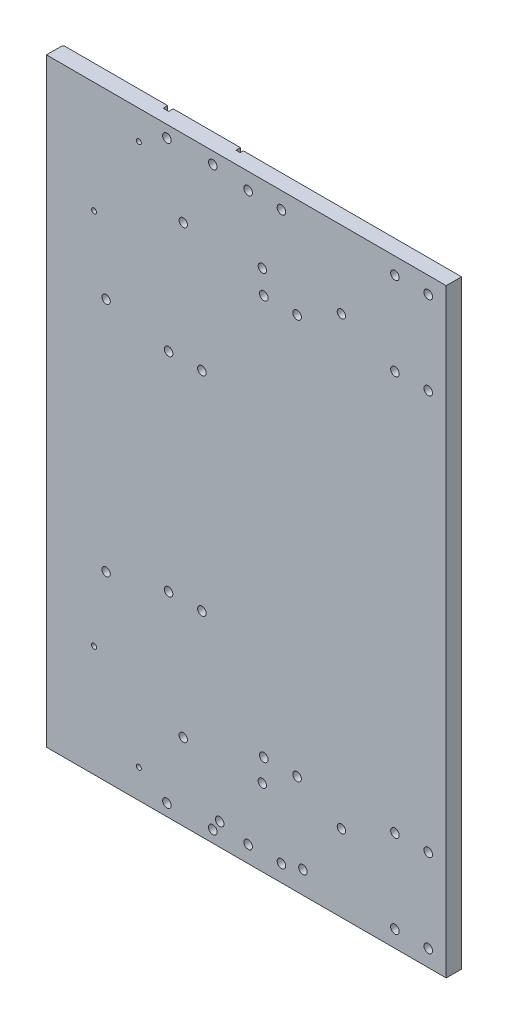
SolidWorks part; units mm, degrees
ref_plane "Front" through (0, 0, 0) normal (0, 0, 1) x (1, 0, 0)
ref_plane "Top" through (0, 0, 0) normal (0, 1, 0) x (1, 0, 0)
ref_plane "Right" through (0, 0, 0) normal (1, 0, 0) x (0, 0, -1)
sketch "Sketch1" plane through (0, 0, 0) normal (0, 0, 1) x (1, 0, 0)
  line L1 (-152.4, -228.6) -> (152.4, -228.6)
  line L2 (-152.4, -228.6) -> (-152.4, 228.6)
  line L3 (-152.4, 228.6) -> (152.4, 228.6)
  line L4 (152.4, -228.6) -> (152.4, 228.6)
  line L5 (-152.4, -228.6) -> (152.4, 228.6) construction
  line L6 (-152.4, 228.6) -> (152.4, -228.6) construction
  point P0 (0, 0)
  dimension "D1" = 304.8
  dimension "D2" = 457.2
extrude "Extrude1" add sketch "Sketch1" along normal blind 12.7
hole_wizard "5/16-18 Tapped Hole1" positions "3DSketch4" profile "Sketch7" tap size "5/16-18" standard "Ansi Inch" end condition up to next
sketch3d "3DSketch4"
  line L0 (1.364, 215.9, 0) -> (26.764, 215.9, 0) construction
  line L1 (14.064, 215.9, 0) -> (14.064, 92.8691, 0) construction
  line L3 (-152.4, 228.6, 0) -> (-152.4, -228.6, 0) construction
  point P0 (1.364, 215.9, 0)
  point P2 (26.764, 215.9, 0)
  dimension "D1" = 153.764
  dimension "D2" = 25.4
  dimension "D3" = 215.9
sketch "Sketch7" plane through (1.364, 215.9, 0) normal (1, 0, 0) x (0, 1, 0)
  line L0 (0, 0) -> (0, 12.701)
  line L1 (0, 12.701) -> (3.2639, 12.701)
  line L2 (3.2639, 12.701) -> (3.2639, 1.3398)
  line L3 (3.2639, 1.3398) -> (4.6037, 0)
  line L5 (4.6037, 0) -> (0, 0)
  line L6 (-3.2639, 1.3398) -> (-4.6037, 0) construction
  line L11 (0, -6.35) -> (0, 107.95) construction
  dimension "Thru Tap Drill Dia." = 6.5278
  dimension "Thru Tap Drill Depth" = 12.701
  dimension "Near C'Sink Dia." = 9.2075
  dimension "Near C'Sink Angle" = 90
cosmetic thread "Hole Thread9" parameters "D2"=7.9375
cosmetic thread "Hole Thread10" parameters "D2"=7.9375
hole_wizard "1/4 (0.25) Diameter Hole2" positions "3DSketch5" profile "Sketch9" hole size "1/4" standard "Ansi Inch"
sketch3d "3DSketch5"
  line L0 (-117.475, 198.2216, 0) -> (-136.525, 198.2216, 0) construction
  line L1 (-117.475, 198.2216, 0) -> (-117.475, 198.2216, 1.2573) construction
  line L2 (-136.525, 198.2216, 0) -> (-136.525, 198.2216, 1.2573) construction
  point P0 (-127, 198.2216, 0)
sketch "Sketch9" plane through (-127, 198.2216, 0) normal (1, 0, 0) x (0, 1, 0)
  line L0 (0, 0) -> (0, 12.701)
  line L1 (0, 12.701) -> (3.175, 12.701)
  line L2 (3.175, 12.701) -> (3.175, 0.381)
  line L3 (3.175, 0.381) -> (3.556, 0)
  line L5 (3.556, 0) -> (0, 0)
  line L6 (-3.175, 0.381) -> (-3.556, 0) construction
  line L11 (0, -6.35) -> (0, 107.95) construction
  dimension "Thru Hole Dia." = 6.35
  dimension "Thru Hole Depth" = 12.701
  dimension "Near C'Sink Dia." = 7.112
  dimension "Near C'Sink Angle" = 90
mirror "Mirror2" about plane through (0, 0, 0) normal (0, 1, 0) of "1/4 (0.25) Diameter Hole2", "5/16-18 Tapped Hole1"
sketch "Sketch10" plane through (0, 0, 0) normal (0, 0, -1) x (-1, 0, 0)
  line L0 (56.9694, -193.0028) -> (101.6133, -217.2425)
  line L2 (152.4, -188.6) -> (125.1873, -173.8247) construction
  line L4 (101.6133, -217.2425) -> (125.1873, -173.8247) construction
  line L5 (152.4, 228.6) -> (152.4, -228.6) construction
  line L6 (152.4, -228.6) -> (-152.4, -228.6) construction
  dimension "D1" = 61.5
  dimension "D2" = 40
  dimension "D3" = 50.8
  dimension "D4" = 30.9652
  dimension "D5" = 49.4048
extrude "Cut-Extrude-Thin1" cut sketch "Sketch10" against normal blind 6 thin thin type mid plane wall 10.16
sketch "Sketch11" plane through (0, 0, 0) normal (0, 0, -1) x (-1, 0, 0)
  line L0 (23.1752, -133.9492) -> (126.1356, -189.8522) construction
  line L1 (88.6834, -134.5929) -> (93.5313, -125.6642)
  line L2 (133.3273, -158.8326) -> (88.6834, -134.5929)
  line L3 (138.1752, -149.9038) -> (133.3273, -158.8326)
  line L4 (54.5454, -197.4672) -> (99.1894, -221.7069)
  line L5 (99.1894, -221.7069) -> (104.0373, -212.7781)
  line L6 (104.0373, -212.7781) -> (59.3934, -188.5384)
  line L7 (59.3934, -188.5384) -> (54.5454, -197.4672)
  line L8 (54.5454, -197.4672) -> (99.1894, -221.7069)
  line L9 (99.1894, -221.7069) -> (104.0373, -212.7781)
  line L10 (104.0373, -212.7781) -> (59.3934, -188.5384)
  line L11 (59.3934, -188.5384) -> (54.5454, -197.4672)
  line L12 (93.5313, -125.6642) -> (138.1752, -149.9038)
  dimension "D2" = 71.5442
  dimension "D1" = 0
extrude "Cut-Extrude1" cut sketch "Sketch11" against normal blind 6
hole_wizard "#10-24 Tapped Hole1" positions "Sketch13" profile "Sketch12" tap size "#10-24" standard "Ansi Inch" end condition through all
sketch "Sketch13" plane through (0, 0, 6) normal (0, 0, -1) x (-1, 0, 0)
  line L0 (101.6133, -217.2425) -> (81.97, -206.577)
  line L1 (104.0373, -212.7781) -> (99.1894, -221.7069) construction
  line L2 (81.97, -206.577) -> (116.1079, -143.7028) construction
  line L3 (135.7513, -154.3682) -> (116.1079, -143.7028) construction
  line L4 (133.3273, -158.8326) -> (138.1752, -149.9038) construction
  point P0 (81.97, -206.577)
  point P7 (116.1079, -143.7028)
  dimension "D1" = 22.352
sketch "Sketch12" plane through (-81.97, -206.577, 6) normal (1, 0, 0) x (0, 1, 0)
  line L0 (0, 0) -> (0, 6.7)
  line L1 (0, 6.7) -> (1.8986, 6.7)
  line L2 (1.8986, 6.7) -> (1.8986, 1.1494)
  line L3 (1.8986, 1.1494) -> (3.048, 0)
  line L5 (3.048, 0) -> (0, 0)
  line L6 (-1.8986, 1.1493) -> (-3.048, 0) construction
  line L11 (0, -6.35) -> (0, 107.95) construction
  dimension "Thru Tap Drill Dia." = 3.7973
  dimension "Thru Tap Drill Depth" = 6.7
  dimension "Near C'Sink Dia." = 6.096
  dimension "Near C'Sink Angle" = 90
cosmetic thread "Hole Thread11" parameters "D2"=4.826
cosmetic thread "Hole Thread12" parameters "D2"=4.826
fillet "Fillet1" radius 3.175 8 edges at (-133.3273, -158.8326, 3) (-138.1752, -149.9038, 3) (-104.0373, -212.7781, 3) (-99.1894, -221.7069, 3) (-88.6834, -134.5929, 3) (-93.5313, -125.6642, 3) (-59.3934, -188.5384, 3) (-54.5454, -197.4672, 3)
mirror "Mirror3" about plane through (0, 0, 0) normal (0, 1, 0) of "Cut-Extrude-Thin1", "Cut-Extrude1", "#10-24 Tapped Hole1", "Fillet1"
hole_wizard "5/16-18 Tapped Hole2" positions "Sketch15" profile "Sketch14" tap size "5/16-18" standard "Ansi Inch"
sketch "Sketch15" plane through (0, 0, 0) normal (0, 0, -1) x (-1, 0, 0)
  line L0 (-43.18, -211.6) -> (20.32, -211.6) construction
  line L1 (152.4, -228.6) -> (-152.4, -228.6) construction
  line L2 (152.4, 228.6) -> (152.4, -228.6) construction
  point P0 (-43.18, -211.6)
  point P1 (20.32, -211.6)
  dimension "D1" = 63.5
  dimension "D2" = 17
  dimension "D3" = 132.08
sketch "Sketch14" plane through (43.18, -211.6, 0) normal (1, 0, 0) x (0, 1, 0)
  line L0 (0, 0) -> (0, 34.4223)
  line L1 (0, 34.4223) -> (3.2639, 32.4612)
  line L2 (3.2639, 32.4612) -> (3.2639, 1.3399)
  line L3 (3.2639, 1.3399) -> (4.6037, 0)
  line L5 (4.6037, 0) -> (0, 0)
  line L6 (-3.2639, 1.3399) -> (-4.6037, 0) construction
  line L10 (0, 34.4223) -> (-3.2639, 32.4612) construction
  line L11 (0, -6.35) -> (0, 107.95) construction
  dimension "Tap Drill Dia." = 6.5278
  dimension "Tap Drill Depth" = 32.4612
  dimension "Near C'Sink Dia." = 9.2075
  dimension "Near C'Sink Angle" = 90
  dimension "Drill Angle" = 118
cosmetic thread "Hole Thread13" parameters "D1"=12.7, "D2"=7.9375
cosmetic thread "Hole Thread14" parameters "D1"=12.7, "D2"=7.9375
hole_wizard "5/16-18 Tapped Hole3" positions "Sketch17" profile "Sketch16" tap size "5/16-18" standard "Ansi Inch" end condition through all
sketch "Sketch17" plane through (0, 0, 0) normal (0, 0, -1) x (-1, 0, 0)
  line L0 (-113.3, 152.4) -> (-113.3, -152.4) construction
  line L1 (-113.3, 0) -> (0, 0) construction
  line L2 (-113.3, 215.9) -> (-113.3, -215.9) construction
  line L3 (-152.4, 228.6) -> (152.4, 228.6) construction
  line L4 (-152.4, -228.6) -> (-152.4, 228.6) construction
  point P0 (-113.3, 215.9)
  point P1 (-138.7, 215.9)
  point P3 (-113.3, 152.4)
  point P5 (-138.7, 152.4)
  point P7 (-113.3, -152.4)
  point P9 (-138.7, -152.4)
  point P11 (-113.3, -215.9)
  point P13 (-138.7, -215.9)
  dimension "D1" = 12.7
  dimension "D2" = 76.2
  dimension "D3" = 13.7
  dimension "D4" = 39.1
sketch "Sketch16" plane through (113.3, 215.9, 0) normal (1, 0, 0) x (0, 1, 0)
  line L0 (0, 0) -> (0, 12.7)
  line L1 (0, 12.7) -> (3.2639, 12.7)
  line L2 (3.2639, 12.7) -> (3.2639, 1.3398)
  line L3 (3.2639, 1.3398) -> (4.6037, 0)
  line L5 (4.6037, 0) -> (0, 0)
  line L6 (-3.2639, 1.3398) -> (-4.6037, 0) construction
  line L11 (0, -6.35) -> (0, 107.95) construction
  dimension "Thru Tap Drill Dia." = 6.5278
  dimension "Thru Tap Drill Depth" = 12.7
  dimension "Near C'Sink Dia." = 9.2075
  dimension "Near C'Sink Angle" = 90
cosmetic thread "Hole Thread15" parameters "D2"=7.9375
cosmetic thread "Hole Thread16" parameters "D2"=7.9375
cosmetic thread "Hole Thread17" parameters "D2"=7.9375
cosmetic thread "Hole Thread18" parameters "D2"=7.9375
cosmetic thread "Hole Thread19" parameters "D2"=7.9375
cosmetic thread "Hole Thread20" parameters "D2"=7.9375
cosmetic thread "Hole Thread21" parameters "D2"=7.9375
cosmetic thread "Hole Thread22" parameters "D2"=7.9375
hole_wizard "5/16-18 Tapped Hole4" positions "Sketch19" profile "Sketch18" tap size "5/16-18" standard "Ansi Inch"
sketch "Sketch19" plane through (0, 0, 0) normal (0, 0, -1) x (-1, 0, 0)
  line L0 (-13.3, 152.4) -> (-13.3, -152.4) construction
  line L1 (0, 0) -> (-13.3, 0) construction
  line L2 (-152.4, 228.6) -> (152.4, 228.6) construction
  line L3 (-152.4, -228.6) -> (-152.4, 228.6) construction
  point P0 (-38.7, 152.4)
  point P1 (-13.3, 152.4)
  point P3 (-38.7, -152.4)
  point P5 (-13.3, -152.4)
  dimension "D1" = 76.2
  dimension "D2" = 25.4
  dimension "D3" = 113.7
sketch "Sketch18" plane through (38.7, 152.4, 0) normal (1, 0, 0) x (0, 1, 0)
  line L0 (0, 0) -> (0, 34.4223)
  line L1 (0, 34.4223) -> (3.2639, 32.4612)
  line L2 (3.2639, 32.4612) -> (3.2639, 1.3399)
  line L3 (3.2639, 1.3399) -> (4.6037, 0)
  line L5 (4.6037, 0) -> (0, 0)
  line L6 (-3.2639, 1.3399) -> (-4.6037, 0) construction
  line L10 (0, 34.4223) -> (-3.2639, 32.4612) construction
  line L11 (0, -6.35) -> (0, 107.95) construction
  dimension "Tap Drill Dia." = 6.5278
  dimension "Tap Drill Depth" = 32.4612
  dimension "Near C'Sink Dia." = 9.2075
  dimension "Near C'Sink Angle" = 90
  dimension "Drill Angle" = 118
cosmetic thread "Hole Thread23" parameters "D1"=12.7, "D2"=7.9375
cosmetic thread "Hole Thread24" parameters "D1"=12.7, "D2"=7.9375
cosmetic thread "Hole Thread25" parameters "D1"=12.7, "D2"=7.9375
cosmetic thread "Hole Thread26" parameters "D1"=12.7, "D2"=7.9375
hole_wizard "5/16-18 Tapped Hole5" positions "Sketch21" profile "Sketch20" tap size "5/16-18" standard "Ansi Inch"
sketch "Sketch21" plane through (0, 0, 0) normal (0, 0, -1) x (-1, 0, 0)
  line L0 (33.8966, 79.375) -> (33.8966, -79.375) construction
  line L1 (0, 0) -> (33.8966, 0) construction
  line L2 (-152.4, -228.6) -> (-152.4, 228.6) construction
  line L3 (-152.4, 228.6) -> (152.4, 228.6) construction
  point P0 (33.8966, 79.375)
  point P1 (59.2966, 79.375)
  point P3 (33.8966, -79.375)
  point P5 (59.2966, -79.375)
  dimension "D1" = 25.4
  dimension "D2" = 186.2966
  dimension "D3" = 149.225
sketch "Sketch20" plane through (-33.8966, 79.375, 0) normal (1, 0, 0) x (0, 1, 0)
  line L0 (0, 0) -> (0, 34.4223)
  line L1 (0, 34.4223) -> (3.2639, 32.4612)
  line L2 (3.2639, 32.4612) -> (3.2639, 1.3398)
  line L3 (3.2639, 1.3398) -> (4.6037, 0)
  line L5 (4.6037, 0) -> (0, 0)
  line L6 (-3.2639, 1.3398) -> (-4.6037, 0) construction
  line L10 (0, 34.4223) -> (-3.2639, 32.4612) construction
  line L11 (0, -6.35) -> (0, 107.95) construction
  dimension "Tap Drill Dia." = 6.5278
  dimension "Tap Drill Depth" = 32.4612
  dimension "Near C'Sink Dia." = 9.2075
  dimension "Near C'Sink Angle" = 90
  dimension "Drill Angle" = 118
cosmetic thread "Hole Thread27" parameters "D1"=12.7, "D2"=7.9375
cosmetic thread "Hole Thread28" parameters "D1"=12.7, "D2"=7.9375
cosmetic thread "Hole Thread29" parameters "D1"=12.7, "D2"=7.9375
cosmetic thread "Hole Thread30" parameters "D1"=12.7, "D2"=7.9375
hole_wizard "1/4 (0.25) Diameter Hole3" positions "Sketch23" profile "Sketch22" hole size "1/4" standard "Ansi Inch" end condition through all
sketch "Sketch23" plane through (0, 0, 0) normal (0, 0, -1) x (-1, 0, 0)
  line L0 (106.9213, 90) -> (106.9213, -90) construction
  line L1 (106.9213, 0) -> (0, 0) construction
  line L3 (152.4, 228.6) -> (152.4, -228.6) construction
  line L4 (48.1203, 170) -> (48.1203, -170) construction
  line L5 (0, 0) -> (48.1203, 0) construction
  point P0 (106.9213, 90)
  point P1 (106.9213, -90)
  point P16 (48.1203, 170)
  point P18 (48.1203, -170)
  point P28 (-12.1793, 170)
  point P30 (-72.4789, 170)
  point P32 (-12.1793, -170)
  point P34 (-72.4789, -170)
  dimension "D1" = 180
  dimension "D2" = 45.4787
  dimension "D3" = 340
  dimension "D4" = 104.2797
  dimension "D5" = 164.5793
  dimension "D6" = 224.8789
sketch "Sketch22" plane through (-106.9213, 90, 0) normal (1, 0, 0) x (0, 1, 0)
  line L0 (0, 0) -> (0, 12.7)
  line L1 (0, 12.7) -> (3.175, 12.7)
  line L2 (3.175, 12.7) -> (3.175, 0.381)
  line L3 (3.175, 0.381) -> (3.556, 0)
  line L5 (3.556, 0) -> (0, 0)
  line L6 (-3.175, 0.381) -> (-3.556, 0) construction
  line L11 (0, -6.35) -> (0, 107.95) construction
  dimension "Thru Hole Dia." = 6.35
  dimension "Thru Hole Depth" = 12.7
  dimension "Near C'Sink Dia." = 7.112
  dimension "Near C'Sink Angle" = 90
hole_wizard "5/16-18 Tapped Hole6" positions "Sketch25" profile "Sketch24" tap size "5/16-18" standard "Ansi Inch" end condition through all
sketch "Sketch25" plane through (0, 0, 0) normal (0, 0, -1) x (-1, 0, 0)
  line L0 (25.5657, -219.6) -> (60.5657, -219.6) construction
  line L1 (43.0657, -219.6) -> (43.0657, -228.6) construction
  line L2 (152.4, -228.6) -> (-152.4, -228.6) construction
  line L3 (152.4, 228.6) -> (152.4, -228.6) construction
  point P0 (25.5657, -219.6)
  point P1 (60.5657, -219.6)
  dimension "D1" = 109.3343
  dimension "D2" = 9
  dimension "D3" = 35
sketch "Sketch24" plane through (-25.5657, -219.6, 0) normal (1, 0, 0) x (0, 1, 0)
  line L0 (0, 0) -> (0, 12.7)
  line L1 (0, 12.7) -> (3.2639, 12.7)
  line L2 (3.2639, 12.7) -> (3.2639, 1.3398)
  line L3 (3.2639, 1.3398) -> (4.6037, 0)
  line L5 (4.6037, 0) -> (0, 0)
  line L6 (-3.2639, 1.3398) -> (-4.6037, 0) construction
  line L11 (0, -6.35) -> (0, 107.95) construction
  dimension "Thru Tap Drill Dia." = 6.5278
  dimension "Thru Tap Drill Depth" = 12.7
  dimension "Near C'Sink Dia." = 9.2075
  dimension "Near C'Sink Angle" = 90
cosmetic thread "Hole Thread31" parameters "D2"=7.9375
cosmetic thread "Hole Thread32" parameters "D2"=7.9375
sketch "Sketch26" plane through (0, 0, 0) normal (0, 0, -1) x (-1, 0, 0)
  line L0 (152.4, -228.6) -> (-152.4, -228.6) construction
  line L1 (13.9769, -228.6) -> (17.1545, -228.6)
  line L2 (13.9769, -228.6) -> (13.9769, -218.0125)
  line L3 (13.9769, -218.0125) -> (17.1545, -218.0125)
  line L4 (17.1545, -228.6) -> (17.1545, -218.0125)
  line L5 (25.5657, -219.6) -> (60.5657, -219.6) construction
  line L6 (43.0657, -219.6) -> (43.0657, -228.6) construction
  line L7 (68.9769, -228.6) -> (68.9769, -218.0125)
  line L8 (72.1545, -218.0125) -> (68.9769, -218.0125)
  line L9 (72.1545, -228.6) -> (72.1545, -218.0125)
  line L10 (72.1545, -228.6) -> (68.9769, -228.6)
  line L11 (15.5657, -228.6) -> (15.5657, -218.0125) construction
  dimension "D1" = 27.5
  dimension "D2" = 3.1775
  dimension "D3" = 10.5875
extrude "Cut-Extrude2" cut sketch "Sketch26" against normal blind 3.429
sketch "Sketch27" plane through (0, 0, 0) normal (0, 0, -1) x (-1, 0, 0)
  line L4 (72.1545, -218.0125) -> (68.9769, -218.0125) construction
  line L6 (152.4, -228.6) -> (72.1545, -228.6) construction
  line L8 (68.4769, -229.1) -> (72.6545, -229.1)
  line L9 (72.6545, -229.1) -> (72.6545, -217.5125)
  line L10 (72.6545, -217.5125) -> (68.4769, -217.5125)
  line L11 (68.4769, -217.5125) -> (68.4769, -229.1)
  line L12 (68.4769, -228.6) -> (72.6545, -228.6)
  line L13 (72.6545, -228.6) -> (72.6545, -218.0125)
  line L14 (72.6545, -218.0125) -> (68.4769, -218.0125)
  line L15 (68.4769, -218.0125) -> (68.4769, -228.6)
  dimension "D1" = 0.5
extrude "Cut-Extrude3" cut sketch "Sketch27" against normal up to surface (3.429 mm away) up to face at (-70.5657, -223.3062, 3.429)
mirror "Mirror4" about plane through (0, 0, 0) normal (0, 1, 0) of "5/16-18 Tapped Hole6", "Cut-Extrude2", "Cut-Extrude3"
fillet "Fillet2" radius 1.5875 8 edges at (-17.1545, -218.0125, 1.7145) (-13.9769, -218.0125, 1.7145) (-72.6545, -218.0125, 1.7145) (-68.4769, -218.0125, 1.7145) (-68.4769, 218.0125, 1.7145) (-72.6545, 218.0125, 1.7145) (-17.1545, 218.0125, 1.7145) (-13.9769, 218.0125, 1.7145)
chamfer "Chamfer1" distance 1.016 angle 45 2 edges at (-152.4, 0, 0) (152.4, 0, 0)
